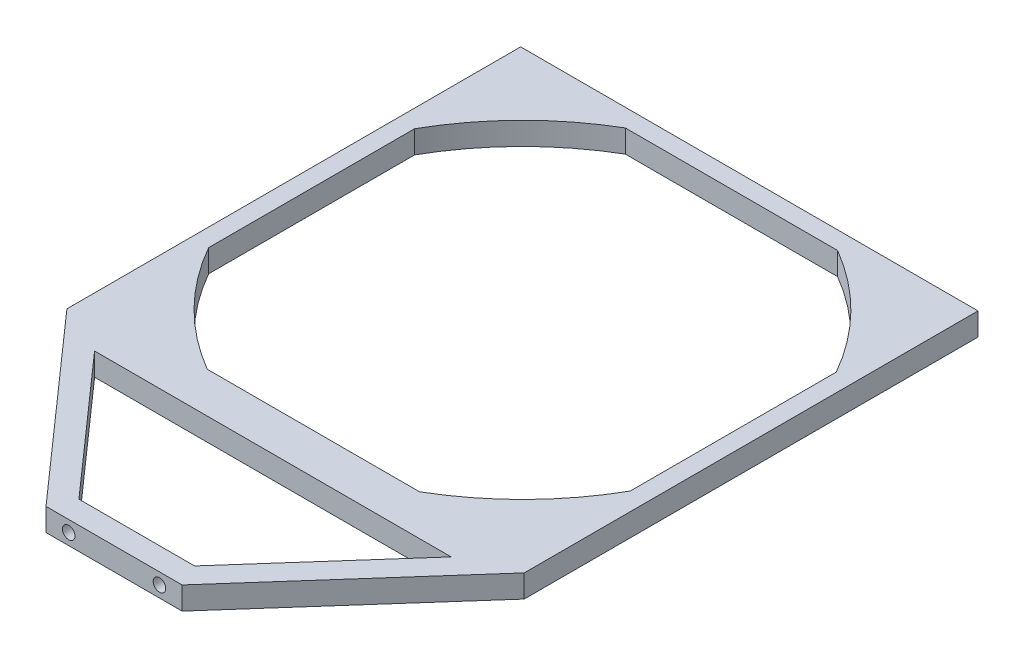
SolidWorks part; units mm, degrees
material "6061-T6 (SS)"
ref_plane "Front Plane" through (0, 0, 0) normal (0, 0, 1) x (1, 0, 0)
ref_plane "Top Plane" through (0, 0, 0) normal (0, 1, 0) x (1, 0, 0)
ref_plane "Right Plane" through (0, 0, 0) normal (1, 0, 0) x (0, 0, -1)
sketch "Sketch2" plane through (0, 0, 0) normal (0, 1, 0) x (1, 0, 0)
  line L0 (-64, -63.5) -> (64, -63.5)
  line L1 (-64, 91.5) -> (64, 91.5) construction
  line L2 (-64, 91.5) -> (-64, -70.5) construction
  line L3 (-64, -70.5) -> (64, -70.5) construction
  line L4 (64, 91.5) -> (64, -70.5) construction
  line L5 (64, -63.5) -> (64, 63.5)
  line L6 (64, 63.5) -> (-64, 63.5)
  line L7 (-64, 63.5) -> (-64, -63.5)
  line L8 (0, -760.6915) -> (0, 49239.3085) construction
  line L9 (29.6957, 58.5) -> (-29.6957, 58.5)
  line L10 (-59, 28.8259) -> (-59, -28.8259)
  line L11 (-52.5, -52.5) -> (52.5, 52.5) construction
  line L12 (-52.5, 52.5) -> (52.5, -52.5) construction
  line L13 (59, 28.8259) -> (59, -28.8259)
  line L14 (-29.6957, -58.5) -> (29.6957, -58.5)
  arc A0 (-29.6957, 58.5) -> (-59, 28.8259) centre (10.6066, -10.6066) ccw
  arc A1 (-59, -28.8259) -> (-29.6957, -58.5) centre (10.6066, 10.6066) ccw
  circle A2 centre (0, 0) radius 60 construction
  arc A3 (29.6957, 58.5) -> (59, 28.8259) centre (-10.6066, -10.6066) cw
  arc A4 (59, -28.8259) -> (29.6957, -58.5) centre (-10.6066, 10.6066) cw
  point P12 (0, 63.5)
  point P19 (-52.5, 52.5)
  point P20 (-52.5, -52.5)
  point P21 (52.5, -52.5)
  point P22 (52.5, 52.5)
  point P30 (0, 58.5)
  dimension "D8" = 120
  dimension "D9" = 80
  dimension "D12" = 80
  dimension "D1" = 128
  dimension "D2" = 7
  dimension "D3" = 28
  dimension "D4" = 5
  dimension "D5" = 105
  dimension "D6" = 39
  dimension "D7" = 105
  dimension "D10" = 15
  dimension "D11" = 15
  dimension "D13" = 5
  dimension "D14" = 5
extrude "Boss-Extrude1" add sketch "Sketch2" along normal blind 6.35
sketch "Sketch3" plane through (0, 6.35, 0) normal (0, 1, 0) x (1, 0, 0)
  line L0 (-64, -63.5) -> (-19.05, -114.3)
  line L1 (-19.05, -114.3) -> (19.05, -114.3)
  line L2 (19.05, -114.3) -> (64, -63.5)
  line L3 (0, -63.5) -> (0, -209.5353) construction
  line L4 (-64, -63.5) -> (64, -63.5) construction
  line L5 (-64, -63.5) -> (64, -63.5)
  line L6 (-49.9023, -69.85) -> (-16.1898, -107.95)
  line L7 (-16.1898, -107.95) -> (16.1898, -107.95)
  line L8 (16.1898, -107.95) -> (49.9023, -69.85)
  line L9 (-49.9023, -69.85) -> (49.9023, -69.85)
  point P11 (0, -114.3)
  dimension "D1" = 38.1
  dimension "D2" = 50.8
  dimension "D3" = 6.35
extrude "Boss-Extrude2" add sketch "Sketch3" against normal blind 6.35
hole_wizard "#6-32 Tapped Hole1" positions "Sketch5" profile "Sketch4" tap size "#6-32" standard "Ansi Inch"
sketch "Sketch5" plane through (0, 0, 114.3) normal (0, 0, 1) x (1, 0, 0)
  line L0 (-19.05, 3.175) -> (19.05, 3.175) construction
  line L1 (-19.05, 0) -> (-19.05, 6.35) construction
  line L2 (19.05, 0) -> (19.05, 6.35) construction
  line L4 (-19.05, 0) -> (19.05, 0) construction
  point P0 (-12.7, 3.175)
  point P1 (12.7, 3.175)
  point P12 (0, 0)
  point P15 (0, 0)
  dimension "D1" = 12.7
  dimension "D2" = 12.7
sketch "Sketch4" plane through (-12.7, 3.175, 114.3) normal (1, 0, 0) x (0, -1, 0)
  line L0 (0, 0) -> (0, 10.2107)
  line L1 (0, 10.2107) -> (1.3525, 9.398)
  line L2 (1.3525, 9.398) -> (1.3525, 7.112)
  line L3 (1.3525, 7.112) -> (1.7526, 7.112)
  line L4 (1.7526, 7.112) -> (1.7526, 0)
  line L5 (1.7526, 0) -> (0, 0)
  line L10 (0, 10.2107) -> (-1.3526, 9.398) construction
  line L11 (0, -6.35) -> (0, 107.95) construction
  dimension "Tap Drill Dia." = 2.7051
  dimension "Tap Drill Depth" = 9.398
  dimension "Thread Major Dia." = 3.5052
  dimension "Thread Depth" = 7.112
  dimension "Drill Angle" = 118
